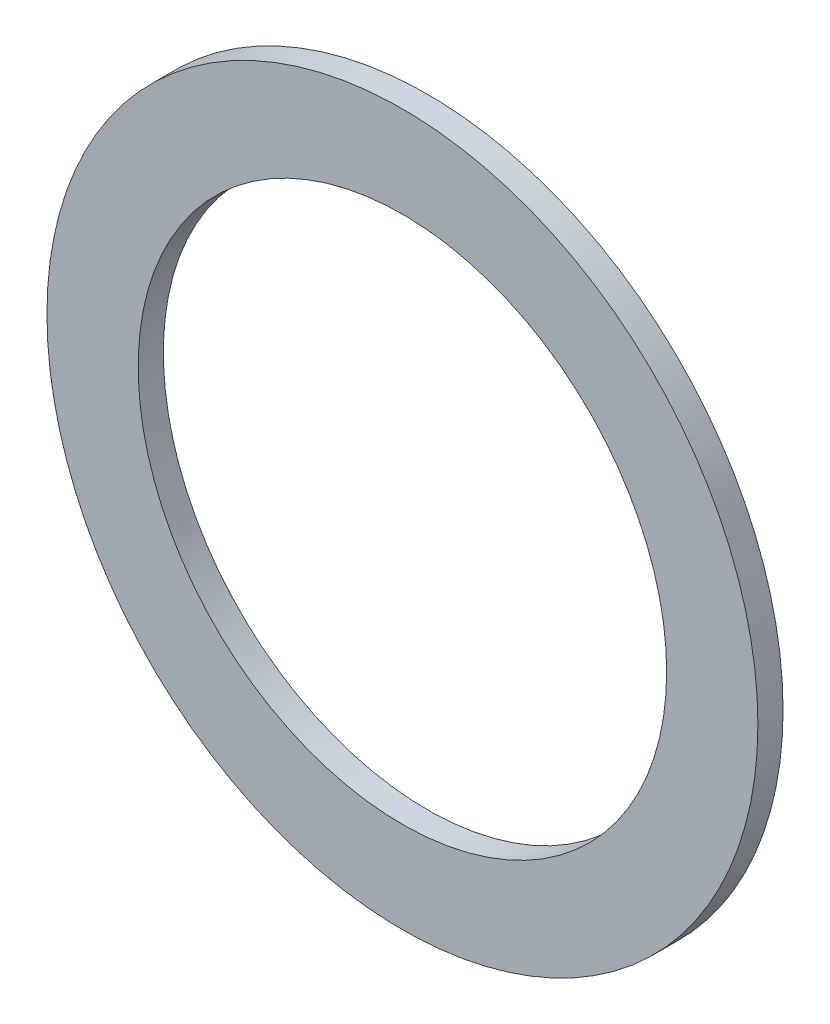
SolidWorks part; units mm, degrees
ref_plane "Plane1" through (0, 0, 0) normal (0, 0, 1) x (1, 0, 0)
ref_plane "Plane2" through (0, 0, 0) normal (0, 1, 0) x (1, 0, 0)
ref_plane "Plane3" through (0, 0, 0) normal (1, 0, 0) x (0, 0, -1)
sketch "Sketch1" plane through (0, 0, 0) normal (0, 0, 1) x (1, 0, 0)
  circle A0 centre (0, 0) radius 14.351
  circle A1 centre (0, 0) radius 10.668
  dimension "D1" = 21.336
  dimension "D2" = 28.702
extrude "Base-Extrude" add sketch "Sketch1" along normal blind 1.016
